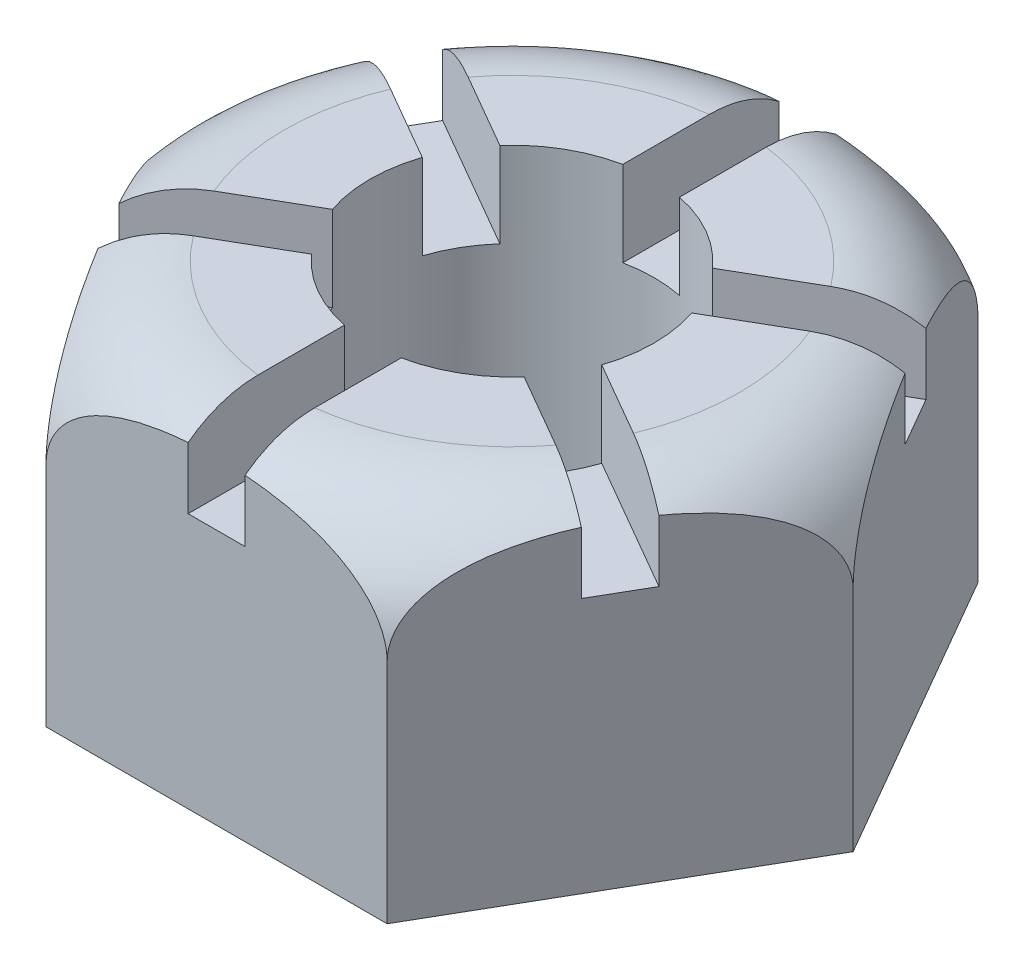
SolidWorks part; units mm, degrees
ref_plane "Front Plane" through (0, 0, 0) normal (0, 0, 1) x (1, 0, 0)
ref_plane "Top Plane" through (0, 0, 0) normal (0, 1, 0) x (1, 0, 0)
ref_plane "Right Plane" through (0, 0, 0) normal (1, 0, 0) x (0, 0, -1)
sketch "Sketch1" plane through (0, 0, 0) normal (0, 1, 0) x (1, 0, 0)
  line L1 (60.0444, 0) -> (30.0222, 52)
  line L2 (30.0222, 52) -> (-30.0222, 52)
  line L3 (-30.0222, 52) -> (-60.0444, 0)
  line L4 (-60.0444, 0) -> (-30.0222, -52)
  line L5 (-30.0222, -52) -> (30.0222, -52)
  line L6 (30.0222, -52) -> (60.0444, 0)
  circle A0 centre (0, 0) radius 52 construction
  circle A1 centre (0, 0) radius 25
  dimension "D2" = 50
  dimension "D1" = 104
extrude "Boss-Extrude1" add sketch "Sketch1" along normal blind 60
sketch "Sketch2" plane through (0, 0, 0) normal (0, 1, 0) x (1, 0, 0)
  line L13 (-60.0444, 0) -> (-30.0222, -52) construction
  line L14 (-30.0222, -52) -> (30.0222, -52) construction
  line L15 (30.0222, -52) -> (60.0444, 0) construction
  line L16 (60.0444, 0) -> (30.0222, 52) construction
  line L17 (30.0222, 52) -> (-30.0222, 52) construction
  line L18 (-30.0222, 52) -> (-60.0444, 0) construction
  line L19 (-47.5333, -21.6699) -> (-42.5333, -30.3301)
  line L20 (-5, -52) -> (5, -52)
  line L21 (42.5333, -30.3301) -> (47.5333, -21.6699)
  line L22 (47.5333, 21.6699) -> (42.5333, 30.3301)
  line L23 (5, 52) -> (-5, 52)
  line L24 (-42.5333, 30.3301) -> (-47.5333, 21.6699)
  line L28 (-23.7132, 7.9173) -> (-47.5333, 21.6699)
  line L29 (-18.7132, 16.5776) -> (-42.5333, 30.3301)
  line L30 (-5, 24.4949) -> (-5, 52)
  line L31 (0, 25) -> (0, 52) construction
  line L32 (5, 24.4949) -> (5, 52)
  line L33 (18.7132, 16.5776) -> (42.5333, 30.3301)
  line L34 (23.7132, 7.9173) -> (47.5333, 21.6699)
  line L35 (23.7132, -7.9173) -> (47.5333, -21.6699)
  line L36 (18.7132, -16.5776) -> (42.5333, -30.3301)
  line L37 (5, -24.4949) -> (5, -52)
  line L38 (-5, -24.4949) -> (-5, -52)
  line L39 (-18.7132, -16.5776) -> (-42.5333, -30.3301)
  line L40 (-23.7132, -7.9173) -> (-47.5333, -21.6699)
  circle A0 centre (0, 0) radius 25 construction
  arc A1 (18.7132, -16.5776) -> (23.7132, -7.9173) centre (0, 0) ccw
  arc A2 (23.7132, 7.9173) -> (18.7132, 16.5776) centre (0, 0) ccw
  arc A3 (5, 24.4949) -> (-5, 24.4949) centre (0, 0) ccw
  arc A4 (-18.7132, 16.5776) -> (-23.7132, 7.9173) centre (0, 0) ccw
  arc A5 (-23.7132, -7.9173) -> (-18.7132, -16.5776) centre (0, 0) ccw
  arc A6 (-5, -24.4949) -> (5, -24.4949) centre (0, 0) ccw
  point P0 (0, 0)
  point P33 (0, 0)
  dimension "D2" = 27.5051
  dimension "D1" = 10
extrude "Cut-Extrude1" cut sketch "Sketch2" along normal up to next from offset 45
sketch "Sketch3" plane through (0, 0, 0) normal (0, 0, 1) x (1, 0, 0)
  line L0 (60.0444, 60) -> (60.0444, 0) construction
  line L1 (60.0444, 40) -> (60.0444, 60)
  line L2 (40.0444, 60) -> (60.0444, 60)
  line L4 (0, 0) -> (0, -11.6731) construction
  arc A0 (60.0444, 40) -> (40.0444, 60) centre (40.0444, 40) ccw
  dimension "D1" = 20
revolve "Cut-Revolve1" cut sketch "Sketch3" angle 360 about L4
